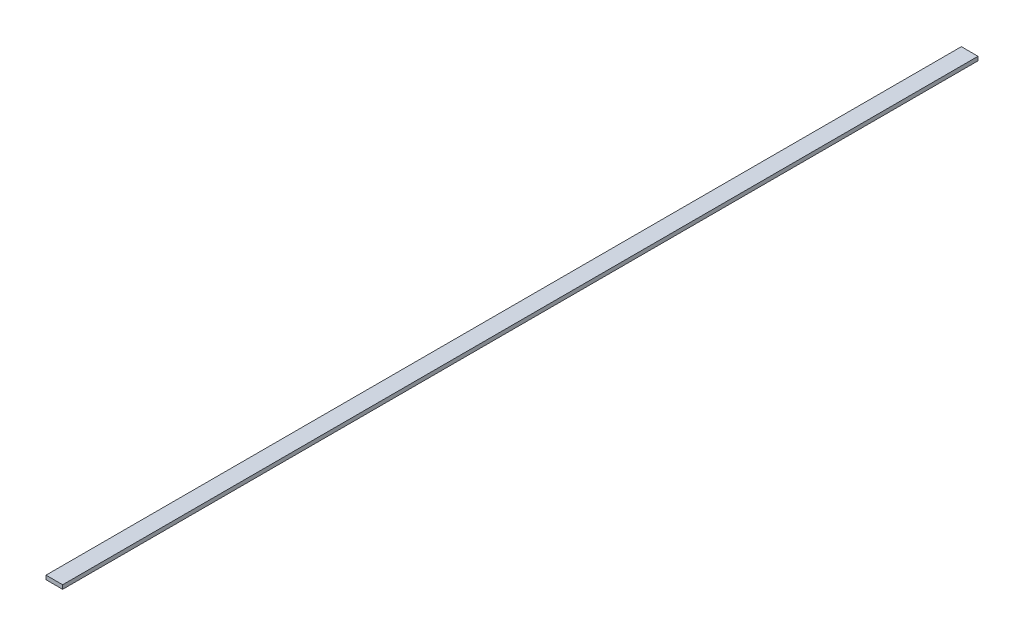
SolidWorks part; units mm, degrees
material "Plain Carbon Steel"
ref_plane "Front Plane" through (0, 0, 0) normal (0, 0, 1) x (1, 0, 0)
ref_plane "Top Plane" through (0, 0, 0) normal (0, 1, 0) x (1, 0, 0)
ref_plane "Right Plane" through (0, 0, 0) normal (1, 0, 0) x (0, 0, -1)
sketch "Sketch1" plane through (0, 0, 0) normal (0, 0, 1) x (1, 0, 0)
  line L1 (0, 0) -> (6.35, 0)
  line L2 (0, 0) -> (0, 1.5189)
  line L3 (0, 1.5189) -> (6.35, 1.5189)
  line L4 (6.35, 0) -> (6.35, 1.5189)
  dimension "D1" = 6.35
  dimension "D2" = 1.5189
extrude "Boss-Extrude1" add sketch "Sketch1" along normal blind 349.25
